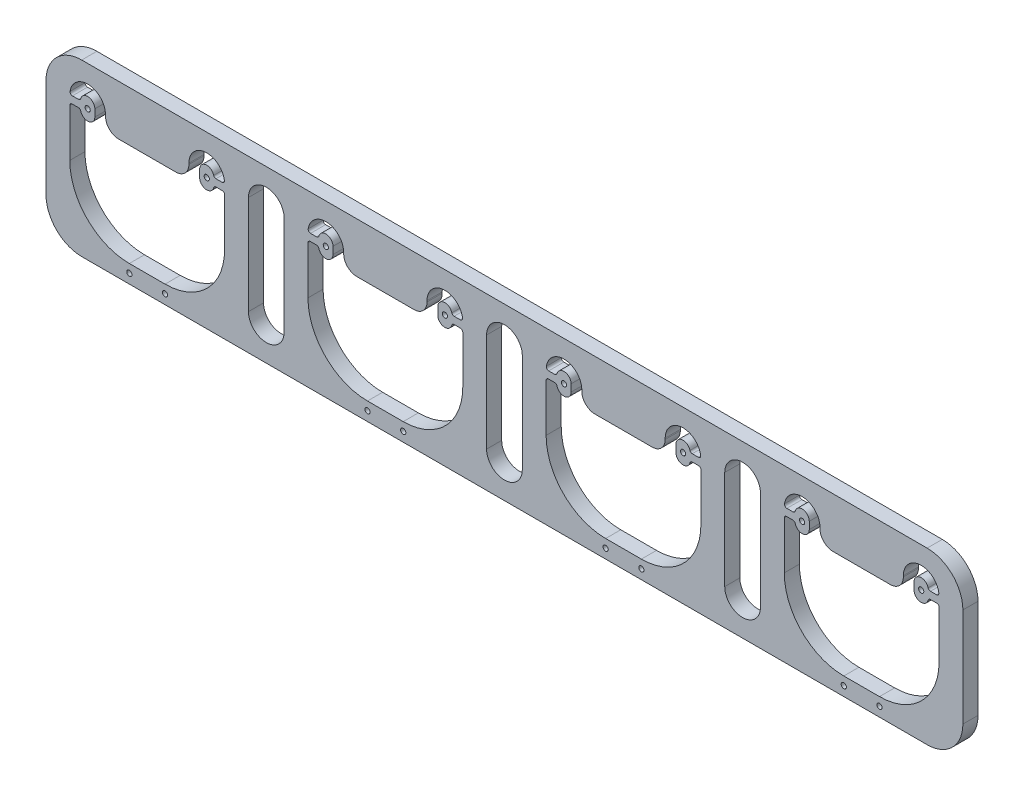
SolidWorks part; units mm, degrees
ref_plane "Front Plane" through (0, 0, 0) normal (0, 0, 1) x (1, 0, 0)
ref_plane "Top Plane" through (0, 0, 0) normal (0, 1, 0) x (1, 0, 0)
ref_plane "Right Plane" through (0, 0, 0) normal (1, 0, 0) x (0, 0, -1)
sketch "Sketch1" plane through (0, 0, 0) normal (0, 0, 1) x (1, 0, 0)
  line L0 (-25.796, 10.9144) -> (-25.796, 28.9144)
  line L5 (39.204, 10.9144) -> (39.204, 28.9144)
  line L7 (24.204, 34.9144) -> (24.204, 34.4144)
  line L8 (-10.796, 34.9144) -> (-10.796, 34.4144)
  line L10 (74.204, 10.9144) -> (74.204, 28.9144)
  line L13 (-0.796, -14.0856) -> (14.204, -14.0856)
  line L14 (-15.296, 34.9144) -> (-15.296, 31.9144)
  line L18 (28.704, 34.9144) -> (28.704, 31.9144)
  line L19 (-25.796, 30.9144) -> (-25.796, 28.9144)
  line L20 (39.204, 30.9144) -> (39.204, 28.9144)
  line L23 (-5.296, 28.9144) -> (18.704, 28.9144)
  line L24 (35.5769, 34.9144) -> (38.1266, 34.9144)
  line L25 (38.204, 31.9144) -> (35.5769, 31.9144)
  line L26 (-22.169, 31.9144) -> (-24.796, 31.9144)
  line L27 (-24.7187, 34.9144) -> (-22.169, 34.9144)
  line L37 (139.204, 10.9144) -> (139.204, 28.9144)
  line L40 (124.204, 34.9144) -> (124.204, 34.4144)
  line L43 (89.204, 34.9144) -> (89.204, 34.4144)
  line L47 (99.204, -14.0856) -> (114.204, -14.0856)
  line L48 (84.704, 34.9144) -> (84.704, 31.9144)
  line L50 (128.704, 34.9144) -> (128.704, 31.9144)
  line L51 (74.204, 30.9144) -> (74.204, 28.9144)
  line L52 (139.204, 30.9144) -> (139.204, 28.9144)
  line L55 (94.704, 28.9144) -> (118.704, 28.9144)
  line L56 (135.5769, 34.9144) -> (138.1266, 34.9144)
  line L57 (138.204, 31.9144) -> (135.5769, 31.9144)
  line L58 (77.831, 31.9144) -> (75.204, 31.9144)
  line L59 (75.2813, 34.9144) -> (77.831, 34.9144)
  line L76 (174.204, 10.9144) -> (174.204, 28.9144)
  line L81 (239.204, 10.9144) -> (239.204, 28.9144)
  line L82 (224.204, 34.9144) -> (224.204, 34.4144)
  line L83 (189.204, 34.9144) -> (189.204, 34.4144)
  line L85 (199.204, -14.0856) -> (214.204, -14.0856)
  line L86 (184.704, 34.9144) -> (184.704, 31.9144)
  line L88 (228.704, 34.9144) -> (228.704, 31.9144)
  line L89 (174.204, 30.9144) -> (174.204, 28.9144)
  line L90 (239.204, 30.9144) -> (239.204, 28.9144)
  line L93 (194.704, 28.9144) -> (218.704, 28.9144)
  line L94 (235.5769, 34.9144) -> (238.1266, 34.9144)
  line L95 (238.204, 31.9144) -> (235.5769, 31.9144)
  line L96 (177.831, 31.9144) -> (175.204, 31.9144)
  line L97 (175.2813, 34.9144) -> (177.831, 34.9144)
  line L114 (274.204, 10.9144) -> (274.204, 28.9144)
  line L119 (339.204, 10.9144) -> (339.204, 28.9144)
  line L120 (324.204, 34.9144) -> (324.204, 34.4144)
  line L121 (289.204, 34.9144) -> (289.204, 34.4144)
  line L123 (299.204, -14.0856) -> (314.204, -14.0856)
  line L124 (284.704, 34.9144) -> (284.704, 31.9144)
  line L126 (328.704, 34.9144) -> (328.704, 31.9144)
  line L127 (274.204, 30.9144) -> (274.204, 28.9144)
  line L128 (339.204, 30.9144) -> (339.204, 28.9144)
  line L131 (294.704, 28.9144) -> (318.704, 28.9144)
  line L132 (335.5769, 34.9144) -> (338.1266, 34.9144)
  line L133 (338.204, 31.9144) -> (335.5769, 31.9144)
  line L134 (277.831, 31.9144) -> (275.204, 31.9144)
  line L135 (275.2813, 34.9144) -> (277.831, 34.9144)
  line L153 (49.204, 34.9144) -> (49.204, -6.5856)
  line L154 (64.204, -6.5856) -> (64.204, 34.9144)
  line L155 (164.204, -6.5856) -> (164.204, 34.9144)
  line L156 (149.204, 34.9144) -> (149.204, -6.5856)
  line L157 (264.204, -6.5856) -> (264.204, 34.9144)
  line L158 (249.204, 34.9144) -> (249.204, -6.5856)
  line L159 (-20.796, 49.9144) -> (334.204, 49.9144)
  line L160 (-35.796, 34.9144) -> (-35.796, -6.5856)
  line L161 (-20.796, -21.5856) -> (334.204, -21.5856)
  line L162 (349.204, -6.5856) -> (349.204, 34.9144)
  arc A2 (-10.796, 34.9144) -> (-25.7068, 36.0683) centre (-18.296, 34.9144) ccw
  arc A3 (24.204, 34.4144) -> (18.704, 28.9144) centre (18.704, 34.4144) cw
  arc A4 (-10.796, 34.4144) -> (-5.296, 28.9144) centre (-5.296, 34.4144) ccw
  arc A5 (39.1147, 36.0683) -> (24.204, 34.9144) centre (31.704, 34.9144) ccw
  arc A8 (14.204, -14.0856) -> (39.204, 10.9144) centre (14.204, 10.9144) ccw
  arc A9 (-25.796, 10.9144) -> (-0.796, -14.0856) centre (-0.796, 10.9144) ccw
  arc A10 (-15.296, 34.9144) -> (-21.2008, 35.6644) centre (-18.296, 34.9144) ccw
  arc A11 (-21.2008, 31.1644) -> (-15.296, 31.9144) centre (-18.296, 31.9144) ccw
  arc A12 (34.6087, 35.6644) -> (28.704, 34.9144) centre (31.704, 34.9144) ccw
  arc A13 (28.704, 31.9144) -> (34.6087, 31.1644) centre (31.704, 31.9144) ccw
  arc A14 (38.204, 31.9144) -> (39.204, 30.9144) centre (38.204, 30.9144) cw
  arc A15 (38.1266, 34.9144) -> (39.1147, 36.0683) centre (38.1266, 35.9144) ccw
  arc A16 (35.5769, 34.9144) -> (34.6087, 35.6644) centre (35.5769, 35.9144) cw
  arc A17 (35.5769, 31.9144) -> (34.6087, 31.1644) centre (35.5769, 30.9144) ccw
  arc A18 (-24.796, 31.9144) -> (-25.796, 30.9144) centre (-24.796, 30.9144) ccw
  arc A19 (-22.169, 31.9144) -> (-21.2008, 31.1644) centre (-22.169, 30.9144) cw
  arc A20 (-22.169, 34.9144) -> (-21.2008, 35.6644) centre (-22.169, 35.9144) ccw
  arc A21 (-24.7187, 34.9144) -> (-25.7068, 36.0683) centre (-24.7187, 35.9144) cw
  arc A40 (89.204, 34.9144) -> (74.2932, 36.0683) centre (81.704, 34.9144) ccw
  arc A41 (124.204, 34.4144) -> (118.704, 28.9144) centre (118.704, 34.4144) cw
  arc A42 (89.204, 34.4144) -> (94.704, 28.9144) centre (94.704, 34.4144) ccw
  arc A43 (139.1147, 36.0683) -> (124.204, 34.9144) centre (131.704, 34.9144) ccw
  arc A46 (114.204, -14.0856) -> (139.204, 10.9144) centre (114.204, 10.9144) ccw
  arc A47 (74.204, 10.9144) -> (99.204, -14.0856) centre (99.204, 10.9144) ccw
  arc A48 (84.704, 34.9144) -> (78.7992, 35.6644) centre (81.704, 34.9144) ccw
  arc A49 (78.7992, 31.1644) -> (84.704, 31.9144) centre (81.704, 31.9144) ccw
  arc A50 (134.6087, 35.6644) -> (128.704, 34.9144) centre (131.704, 34.9144) ccw
  arc A51 (128.704, 31.9144) -> (134.6087, 31.1644) centre (131.704, 31.9144) ccw
  arc A52 (138.204, 31.9144) -> (139.204, 30.9144) centre (138.204, 30.9144) cw
  arc A53 (138.1266, 34.9144) -> (139.1147, 36.0683) centre (138.1266, 35.9144) ccw
  arc A54 (135.5769, 34.9144) -> (134.6087, 35.6644) centre (135.5769, 35.9144) cw
  arc A55 (135.5769, 31.9144) -> (134.6087, 31.1644) centre (135.5769, 30.9144) ccw
  arc A56 (75.204, 31.9144) -> (74.204, 30.9144) centre (75.204, 30.9144) ccw
  arc A57 (77.831, 31.9144) -> (78.7992, 31.1644) centre (77.831, 30.9144) cw
  arc A58 (77.831, 34.9144) -> (78.7992, 35.6644) centre (77.831, 35.9144) ccw
  arc A59 (75.2813, 34.9144) -> (74.2932, 36.0683) centre (75.2813, 35.9144) cw
  arc A78 (189.204, 34.9144) -> (174.2932, 36.0683) centre (181.704, 34.9144) ccw
  arc A79 (224.204, 34.4144) -> (218.704, 28.9144) centre (218.704, 34.4144) cw
  arc A80 (189.204, 34.4144) -> (194.704, 28.9144) centre (194.704, 34.4144) ccw
  arc A81 (239.1147, 36.0683) -> (224.204, 34.9144) centre (231.704, 34.9144) ccw
  arc A84 (214.204, -14.0856) -> (239.204, 10.9144) centre (214.204, 10.9144) ccw
  arc A85 (174.204, 10.9144) -> (199.204, -14.0856) centre (199.204, 10.9144) ccw
  arc A86 (184.704, 34.9144) -> (178.7992, 35.6644) centre (181.704, 34.9144) ccw
  arc A87 (178.7992, 31.1644) -> (184.704, 31.9144) centre (181.704, 31.9144) ccw
  arc A88 (234.6087, 35.6644) -> (228.704, 34.9144) centre (231.704, 34.9144) ccw
  arc A89 (228.704, 31.9144) -> (234.6087, 31.1644) centre (231.704, 31.9144) ccw
  arc A90 (238.204, 31.9144) -> (239.204, 30.9144) centre (238.204, 30.9144) cw
  arc A91 (238.1266, 34.9144) -> (239.1147, 36.0683) centre (238.1266, 35.9144) ccw
  arc A92 (235.5769, 34.9144) -> (234.6087, 35.6644) centre (235.5769, 35.9144) cw
  arc A93 (235.5769, 31.9144) -> (234.6087, 31.1644) centre (235.5769, 30.9144) ccw
  arc A94 (175.204, 31.9144) -> (174.204, 30.9144) centre (175.204, 30.9144) ccw
  arc A95 (177.831, 31.9144) -> (178.7992, 31.1644) centre (177.831, 30.9144) cw
  arc A96 (177.831, 34.9144) -> (178.7992, 35.6644) centre (177.831, 35.9144) ccw
  arc A97 (175.2813, 34.9144) -> (174.2932, 36.0683) centre (175.2813, 35.9144) cw
  arc A116 (289.204, 34.9144) -> (274.2932, 36.0683) centre (281.704, 34.9144) ccw
  arc A117 (324.204, 34.4144) -> (318.704, 28.9144) centre (318.704, 34.4144) cw
  arc A118 (289.204, 34.4144) -> (294.704, 28.9144) centre (294.704, 34.4144) ccw
  arc A119 (339.1147, 36.0683) -> (324.204, 34.9144) centre (331.704, 34.9144) ccw
  arc A122 (314.204, -14.0856) -> (339.204, 10.9144) centre (314.204, 10.9144) ccw
  arc A123 (274.204, 10.9144) -> (299.204, -14.0856) centre (299.204, 10.9144) ccw
  arc A124 (284.704, 34.9144) -> (278.7992, 35.6644) centre (281.704, 34.9144) ccw
  arc A125 (278.7992, 31.1644) -> (284.704, 31.9144) centre (281.704, 31.9144) ccw
  arc A126 (334.6087, 35.6644) -> (328.704, 34.9144) centre (331.704, 34.9144) ccw
  arc A127 (328.704, 31.9144) -> (334.6087, 31.1644) centre (331.704, 31.9144) ccw
  arc A128 (338.204, 31.9144) -> (339.204, 30.9144) centre (338.204, 30.9144) cw
  arc A129 (338.1266, 34.9144) -> (339.1147, 36.0683) centre (338.1266, 35.9144) ccw
  arc A130 (335.5769, 34.9144) -> (334.6087, 35.6644) centre (335.5769, 35.9144) cw
  arc A131 (335.5769, 31.9144) -> (334.6087, 31.1644) centre (335.5769, 30.9144) ccw
  arc A132 (275.204, 31.9144) -> (274.204, 30.9144) centre (275.204, 30.9144) ccw
  arc A133 (277.831, 31.9144) -> (278.7992, 31.1644) centre (277.831, 30.9144) cw
  arc A134 (277.831, 34.9144) -> (278.7992, 35.6644) centre (277.831, 35.9144) ccw
  arc A135 (275.2813, 34.9144) -> (274.2932, 36.0683) centre (275.2813, 35.9144) cw
  arc A152 (64.204, 34.9144) -> (49.204, 34.9144) centre (56.704, 34.9144) ccw
  arc A153 (49.204, -6.5856) -> (64.204, -6.5856) centre (56.704, -6.5856) ccw
  arc A154 (164.204, 34.9144) -> (149.204, 34.9144) centre (156.704, 34.9144) ccw
  arc A155 (149.204, -6.5856) -> (164.204, -6.5856) centre (156.704, -6.5856) ccw
  arc A156 (264.204, 34.9144) -> (249.204, 34.9144) centre (256.704, 34.9144) ccw
  arc A157 (249.204, -6.5856) -> (264.204, -6.5856) centre (256.704, -6.5856) ccw
  arc A158 (-20.796, 49.9144) -> (-35.796, 34.9144) centre (-20.796, 34.9144) ccw
  arc A159 (-35.796, -6.5856) -> (-20.796, -21.5856) centre (-20.796, -6.5856) ccw
  arc A160 (334.204, -21.5856) -> (349.204, -6.5856) centre (334.204, -6.5856) ccw
  arc A161 (334.204, 49.9144) -> (349.204, 34.9144) centre (334.204, 34.9144) cw
  circle A162 centre (-18.296, 33.4144) radius 1.0922
  circle A163 centre (31.704, 33.4144) radius 1.0922
  circle A164 centre (14.204, -17.6203) radius 1.0922
  circle A165 centre (-0.796, -17.6203) radius 1.0922
  circle A166 centre (81.704, 33.4144) radius 1.0922
  circle A167 centre (131.704, 33.4144) radius 1.0922
  circle A168 centre (114.204, -17.6203) radius 1.0922
  circle A169 centre (99.204, -17.6203) radius 1.0922
  circle A170 centre (181.704, 33.4144) radius 1.0922
  circle A171 centre (231.704, 33.4144) radius 1.0922
  circle A172 centre (214.204, -17.6203) radius 1.0922
  circle A173 centre (199.204, -17.6203) radius 1.0922
  circle A174 centre (281.704, 33.4144) radius 1.0922
  circle A175 centre (331.704, 33.4144) radius 1.0922
  circle A176 centre (314.204, -17.6203) radius 1.0922
  circle A177 centre (299.204, -17.6203) radius 1.0922
  dimension "D15" = 7.5
  dimension "D16" = 7.5
  dimension "D24" = 25
  dimension "D26" = 65
  dimension "D29" = 3
  dimension "D30" = 3
  dimension "D11" = 5.5
  dimension "D22" = 1
  dimension "D34" = 15
  dimension "D35" = 15
  dimension "D43" = 15
  dimension "D46" = 15
  dimension "D44" = 2.1844
  dimension "D36" = 7.5
  dimension "D38" = 17.5
  dimension "D39" = 17.5
  dimension "D40" = 0
  dimension "D41" = 15
  dimension "D37" = 4
  dimension "D42" = 3
extrude "Boss-Extrude1" add sketch "Sketch1" along normal blind 6.35
